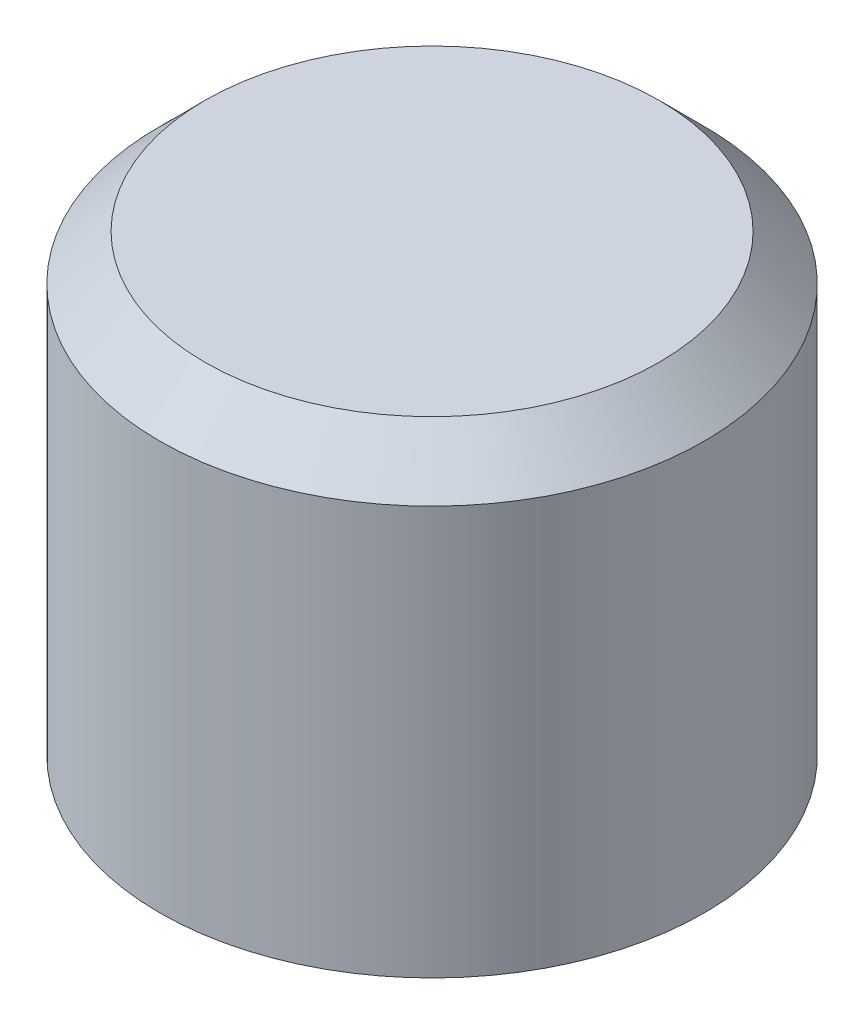
SolidWorks part; units mm, degrees
material "AISI 316 Stainless Steel Sheet (SS)"
ref_plane "Front Plane" through (0, 0, 0) normal (0, 0, 1) x (1, 0, 0)
ref_plane "Top Plane" through (0, 0, 0) normal (0, 1, 0) x (1, 0, 0)
ref_plane "Right Plane" through (0, 0, 0) normal (1, 0, 0) x (0, 0, -1)
sketch "Sketch1" plane through (0, 0, 0) normal (0, 1, 0) x (1, 0, 0)
  circle A0 centre (0, 0) radius 6
  dimension "D1" = 12
extrude "Boss-Extrude1" add sketch "Sketch1" along normal blind 10
chamfer "Chamfer1" distance 1 angle 45 1 edges at (0, 10, 6)
sketch "Sketch2" plane through (0, 0, 0) normal (0, -1, 0) x (1, 0, 0)
  circle A0 centre (0, 0) radius 4
  dimension "D1" = 8
extrude "Cut-Extrude1" cut sketch "Sketch2" against normal blind 7
